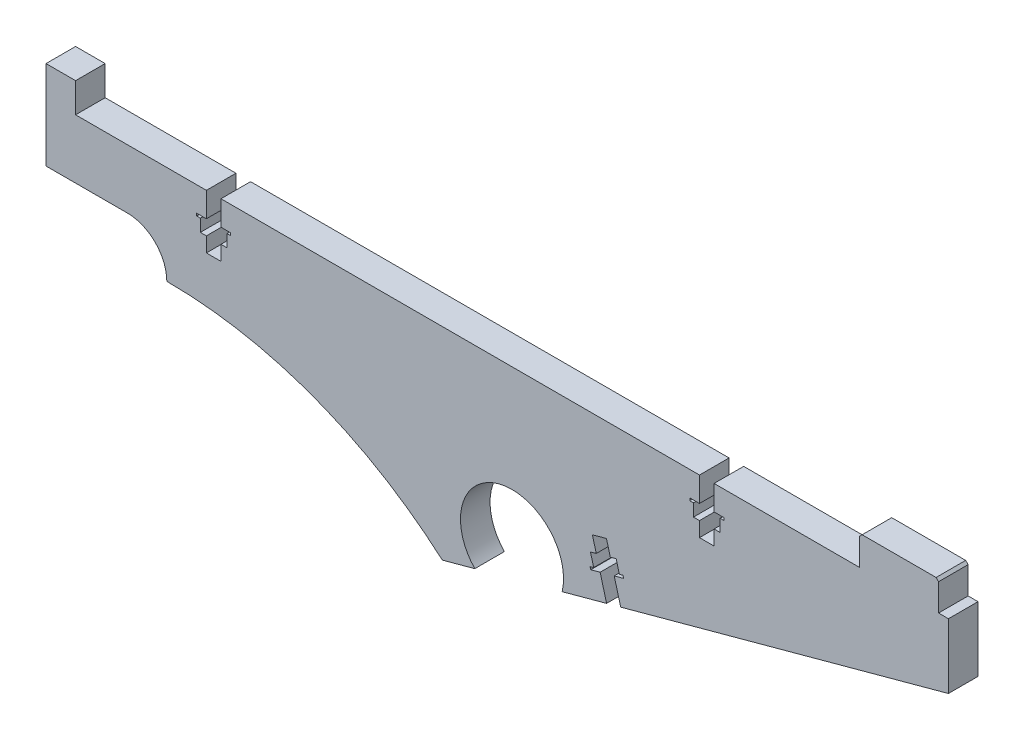
SolidWorks part; units mm, degrees
material "Oak"
ref_plane "Front Plane" through (0, 0, 0) normal (0, 0, 1) x (1, 0, 0)
ref_plane "Top Plane" through (0, 0, 0) normal (0, 1, 0) x (1, 0, 0)
ref_plane "Right Plane" through (0, 0, 0) normal (1, 0, 0) x (0, 0, -1)
sketch "Sketch1" plane through (0, 0, 0) normal (0, 0, 1) x (1, 0, 0)
  line L0 (116.02, 20) -> (116.02, 15)
  line L5 (-16.5, 8) -> (-16.5, 26)
  line L7 (164.5, 26) -> (164.5, 20)
  line L8 (70.4558, -19.231) -> (88.1661, -14.4192) construction
  line L9 (116.02, 15) -> (114.05, 15)
  line L10 (-18, 24.8801) -> (-18, -27.1715) construction
  line L12 (-16.5, 26) -> (-10.5, 26)
  line L13 (114.05, 15) -> (114.05, 14.5)
  line L14 (114.05, 14.5) -> (114.8, 14.5)
  line L15 (114.8, 14.5) -> (114.8, 12)
  line L16 (114.8, 12) -> (116.02, 12)
  line L17 (116.02, 12) -> (116.02, 9)
  line L18 (116.02, 9) -> (118.98, 9)
  line L19 (118.98, 12) -> (118.98, 9)
  line L20 (120.2, 12) -> (118.98, 12)
  line L21 (120.2, 14.5) -> (120.2, 12)
  line L22 (120.95, 14.5) -> (120.2, 14.5)
  line L23 (120.95, 15) -> (120.95, 14.5)
  line L24 (118.98, 15) -> (120.95, 15)
  line L25 (118.98, 20) -> (118.98, 15)
  line L26 (117.5, 20) -> (117.5, 9) construction
  line L27 (88.1661, -14.4192) -> (166.5, 6.8638)
  line L28 (78, -12) -> (79.311, -16.8251) construction
  line L29 (-16.5, 8) -> (0, 8)
  line L30 (17.5, 20) -> (17.5, 9) construction
  line L31 (16.02, 20) -> (16.02, 15)
  line L32 (16.02, 15) -> (14.05, 15)
  line L33 (14.05, 15) -> (14.05, 14.5)
  line L34 (14.05, 14.5) -> (14.8, 14.5)
  line L35 (14.8, 14.5) -> (14.8, 12)
  line L36 (14.8, 12) -> (16.02, 12)
  line L37 (16.02, 12) -> (16.02, 9)
  line L38 (16.02, 9) -> (18.98, 9)
  line L39 (18.98, 12) -> (18.98, 9)
  line L40 (20.2, 12) -> (18.98, 12)
  line L41 (20.2, 14.5) -> (20.2, 12)
  line L42 (20.95, 14.5) -> (20.2, 14.5)
  line L43 (16.02, 20) -> (116.02, 20) construction
  line L44 (164.5, 20) -> (166.5, 20)
  line L45 (-10.5, 26) -> (-10.5, 20)
  line L46 (-10.5, 20) -> (16.02, 20)
  line L47 (166.5, 20) -> (166.5, 6.8638)
  line L48 (63.8707, -21.0201) -> (62.5597, -16.1951) construction
  line L49 (62.5597, -16.1951) -> (78, -12) construction
  line L50 (63.8707, -21.0201) -> (70.4558, -19.231)
  line L51 (20.95, 15) -> (20.95, 14.5)
  line L52 (18.98, 15) -> (20.95, 15)
  line L53 (18.98, 20) -> (18.98, 15)
  line L54 (18.98, 20) -> (116.02, 20)
  line L55 (118.98, 20) -> (148.5, 20)
  line L56 (19.5, -3.7) -> (26.5, -3.7) construction
  line L57 (148.5, 20) -> (148.5, 26)
  line L58 (148.5, 26) -> (164.5, 26)
  line L59 (19.5, -2.7) -> (26.5, -2.7) construction
  line L60 (19.5, -4.7) -> (26.5, -4.7) construction
  circle A0 centre (0, 0) radius 6 construction
  circle A1 centre (78, -12) radius 6 construction
  arc A2 (88.1661, -14.4192) -> (70.4558, -19.231) centre (78, -12) ccw
  arc A3 (63.8707, -21.0201) -> (8, 0) centre (8, -84.7611) ccw
  arc A4 (19.5, -2.7) -> (19.5, -4.7) centre (19.5, -3.7) ccw construction
  arc A5 (26.5, -4.7) -> (26.5, -2.7) centre (26.5, -3.7) ccw construction
  arc A6 (8, 0) -> (0, 8) centre (0, 0) ccw
  point P56 (23, -3.7)
  dimension "D1" = 12
  dimension "D7" = 12
  dimension "D23" = 20.9
  dimension "D19" = 1
  dimension "D4" = 20
  dimension "D5" = 78
  dimension "D6" = 12
  dimension "D8" = 6
  dimension "D9" = 181
  dimension "D14" = 2
  dimension "D15" = 100
  dimension "D16" = 2
  dimension "D17" = 16
  dimension "D18" = 7
  dimension "D20" = 3.7
  dimension "D24" = 5
  dimension "D25" = 16.5
  dimension "D27" = 11
  dimension "D28" = 3
  dimension "D29" = 0.5
  dimension "D30" = 2.5
  dimension "D31" = 2.96
  dimension "D33" = 6.9
  dimension "D34" = 5.4
  dimension "D35" = 28
  dimension "D36" = 16
  dimension "D37" = 6
extrude "Boss-Extrude1" add sketch "Sketch1" along normal blind 6
chamfer "Chamfer1" [suppressed] distance 3 distance2 2
chamfer "Chamfer2" distance 0.5 angle 45 2 edges at (164.5, 26, 3) (148.5, 26, 3)
sketch "Sketch2" plane through (0, 0, 6) normal (0, 0, 1) x (1, 0, 0)
  line L0 (98.6113, -11.5813) -> (95.7272, -0.9661) construction
  line L1 (88.1661, -14.4192) -> (166.5, 6.8638) construction
  line L2 (100.0395, -11.1932) -> (97.1831, -11.9693)
  line L3 (94.2989, -1.3541) -> (97.1554, -0.578)
  line L4 (97.1554, -0.578) -> (97.942, -3.4731)
  line L5 (97.942, -3.4731) -> (99.1193, -3.1532)
  line L6 (99.1193, -3.1532) -> (99.7748, -5.5658)
  line L7 (99.7748, -5.5658) -> (100.4985, -5.3691)
  line L8 (100.4985, -5.3691) -> (100.6296, -5.8516)
  line L9 (100.6296, -5.8516) -> (98.7285, -6.3681)
  line L10 (98.7285, -6.3681) -> (100.0395, -11.1932)
  line L11 (95.8721, -7.1442) -> (97.1831, -11.9693)
  line L12 (93.971, -7.6607) -> (95.8721, -7.1442)
  line L13 (93.8399, -7.1782) -> (93.971, -7.6607)
  line L14 (94.5637, -6.9816) -> (93.8399, -7.1782)
  line L15 (93.9082, -4.569) -> (94.5637, -6.9816)
  line L16 (95.0855, -4.2492) -> (93.9082, -4.569)
  line L17 (94.2989, -1.3541) -> (95.0855, -4.2492)
  line L18 (78, -12) -> (97.3003, -6.7562) construction
  point P21 (78, -12)
  dimension "D1" = 2.96
  dimension "D2" = 6.9
  dimension "D3" = 5.4
  dimension "D4" = 0.5
  dimension "D5" = 2.5
  dimension "D6" = 3
  dimension "D7" = 11
  dimension "D8" = 20
extrude "Cut-Extrude1" cut sketch "Sketch2" against normal through all
equation "\"bed-plate-thickness\"=6"
equation "\"D1@Boss-Extrude1\"=\"y-cross-rib-thickness\""
equation "\"D37@Sketch1\" = \"bed-plate-thickness\""
equation "\"y-cross-rib-thickness\"=6"
equation "\"y-rib-thickness\"=6"
equation "\"x-plate-thickness\"=5"
equation "\"rod-diameter\"=12"
equation "\"t-nut-hole-diameter\"=3"
equation "\"D20@Sketch1\" = 9 - ( 11.6 / 2 ) + .5"
equation "\"D8@Sketch1\"=\"y-rib-thickness\""
